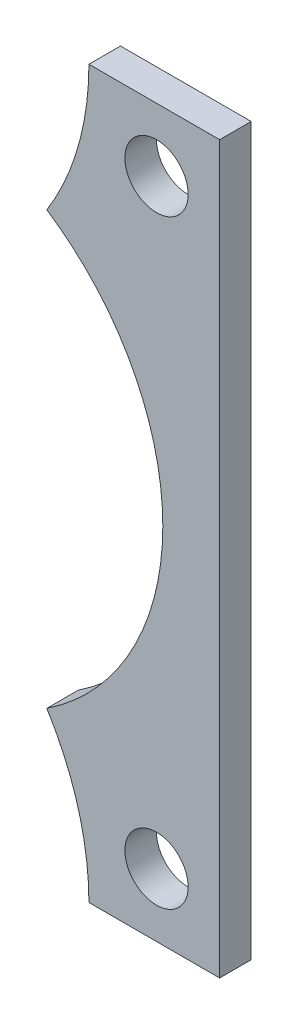
SolidWorks part; units mm, degrees
ref_plane "Front Plane" through (0, 0, 0) normal (0, 0, 1) x (1, 0, 0)
ref_plane "Top Plane" through (0, 0, 0) normal (0, 1, 0) x (1, 0, 0)
ref_plane "Right Plane" through (0, 0, 0) normal (1, 0, 0) x (0, 0, -1)
sketch "Sketch1" plane through (0, 0, 0) normal (0, 0, 1) x (1, 0, 0)
  line L0 (-7.2461, 73.025) -> (-7.2461, -73.025) construction
  line L1 (-19.05, -73.025) -> (19.05, -73.025)
  line L2 (-19.05, -73.025) -> (-19.05, 73.025)
  line L3 (-19.05, 73.025) -> (19.05, 73.025)
  line L4 (19.05, -73.025) -> (19.05, 73.025)
  line L5 (-19.05, -73.025) -> (19.05, 73.025) construction
  line L6 (-19.05, 73.025) -> (19.05, -73.025) construction
  line L7 (-44.45, 20.32) -> (-44.45, -20.32) construction
  line L8 (-44.45, 0) -> (0, 0) construction
  circle A0 centre (-44.45, 0) radius 52.07
  circle A1 centre (6.35, 60.325) radius 6.3627
  circle A2 centre (6.35, -60.325) radius 6.3627
  arc A3 (-7.2461, 73.025) -> (-19.05, 45.4546) centre (-45.3461, 73.025) cw
  circle A4 centre (-44.45, 0) radius 20.32
  arc A5 (-7.2461, 73.025) -> (-44.45, 20.32) centre (-63.1804, 73.025) cw
  arc A6 (-7.2461, -73.025) -> (-44.45, -20.32) centre (-63.1804, -73.025) ccw
  point P0 (0, 0)
  dimension "D2" = 104.14
  dimension "D3" = 12.7254
  dimension "D9" = 38.1
  dimension "D10" = 40.64
  dimension "D1" = 146.05
  dimension "D4" = 12.7
  dimension "D5" = 12.7
  dimension "D6" = 50.8
  dimension "D7" = 38.1
  dimension "D8" = 12.7
extrude "Boss-Extrude1" add sketch "Sketch1" along normal mid plane 6.35 contours A6 L1 L4 L3 A5 A0 A2 A1
